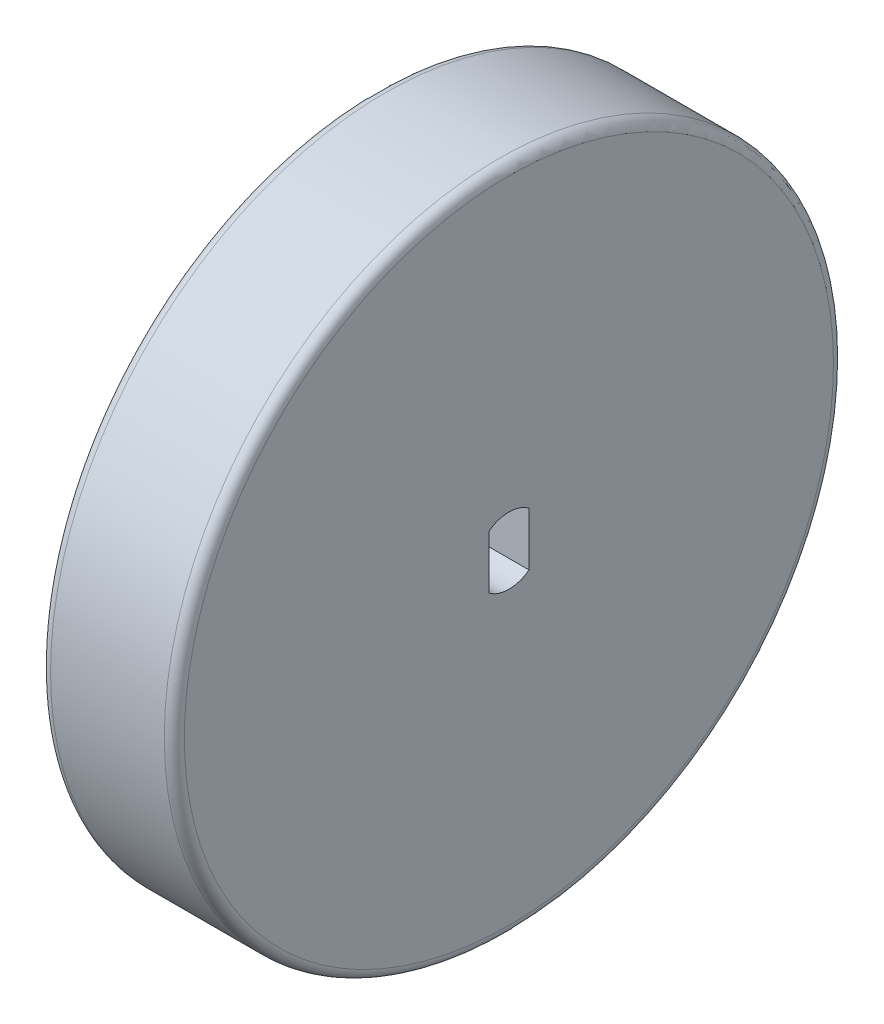
SolidWorks part; units mm, degrees
ref_plane "Front Plane" through (0, 0, 0) normal (0, 0, 1) x (1, 0, 0)
ref_plane "Top Plane" through (0, 0, 0) normal (0, 1, 0) x (1, 0, 0)
ref_plane "Right Plane" through (0, 0, 0) normal (1, 0, 0) x (0, 0, -1)
sketch "Sketch1" plane through (0, 0, 0) normal (1, 0, 0) x (0, 0, -1)
  circle A0 centre (0, 0) radius 25.4
  dimension "D1" = 50.8
extrude "Boss-Extrude1" add sketch "Sketch1" along normal blind 10.16 contours A0
fillet "Fillet1" radius 0.762 2 edges at (10.16, 0, -25.4) (0, 0, -25.4)
sketch "Sketch2" plane through (10.16, 0, 0) normal (1, 0, 0) x (0, 0, -1)
  line L2 (-1.524, -2.032) -> (-1.524, 2.032)
  line L3 (1.524, 2.032) -> (1.524, -2.032)
  arc A0 (-1.524, -2.032) -> (1.524, -2.032) centre (0, 0) ccw
  arc A1 (1.524, 2.032) -> (-1.524, 2.032) centre (0, 0) ccw
  dimension "D1" = 5.08
extrude "Cut-Extrude1" cut sketch "Sketch2" against normal through all
